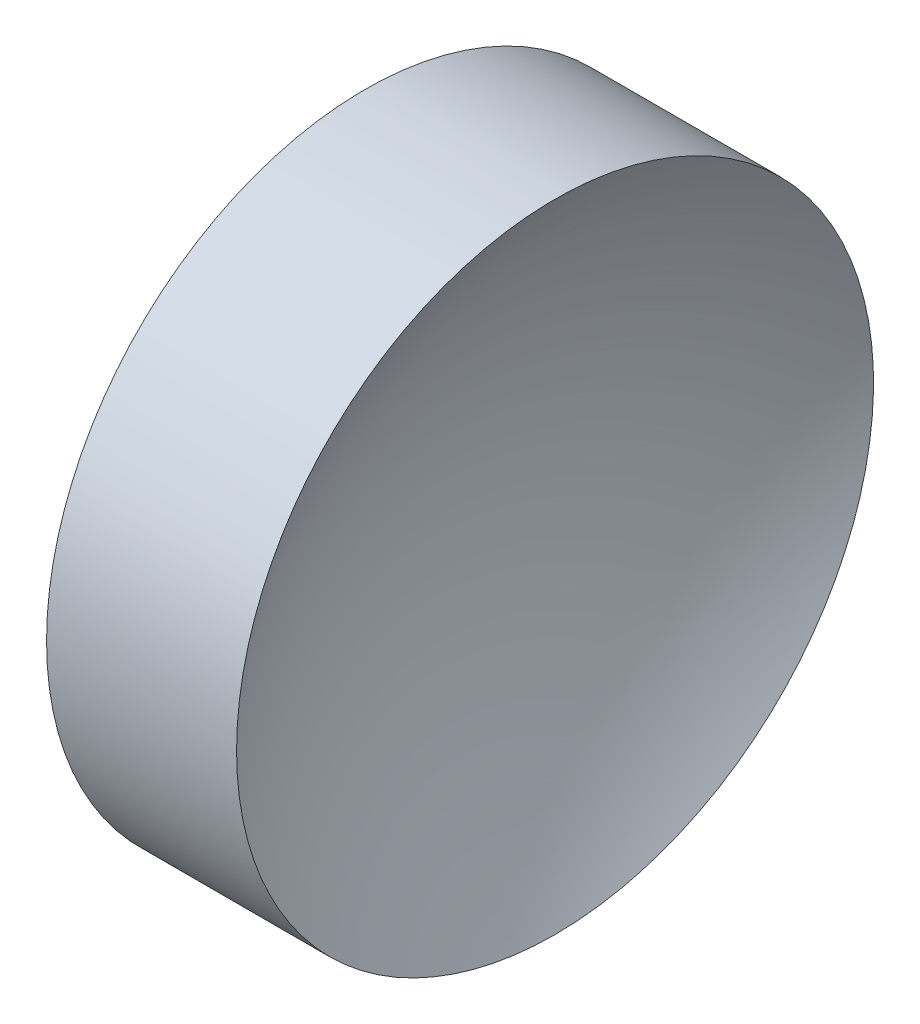
SolidWorks part; units mm, degrees
ref_plane "前视基准面" through (0, 0, 0) normal (0, 0, 1) x (1, 0, 0)
ref_plane "上视基准面" through (0, 0, 0) normal (0, 1, 0) x (1, 0, 0)
ref_plane "右视基准面" through (0, 0, 0) normal (1, 0, 0) x (0, 0, -1)
sketch "草图1" plane through (0, 0, 0) normal (0, 0, 1) x (1, 0, 0)
  line L0 (39.7365, 26.0623) -> (48.2578, 26.0623) construction
  line L1 (41.3658, 26.0623) -> (41.3658, 31.0623)
  line L2 (42.8658, 26.0623) -> (41.3658, 26.0623)
  line L3 (41.3658, 31.0623) -> (44.3489, 31.0623)
  arc A0 (44.3489, 31.0623) -> (42.8658, 26.0623) centre (52.0358, 26.0623) ccw
revolve "旋转1" add sketch "草图1" angle 360 about L0
